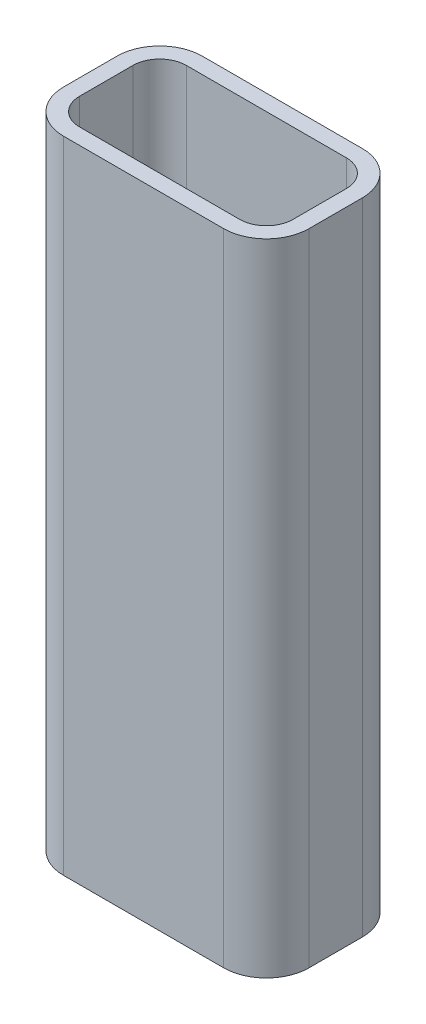
SolidWorks part; units mm, degrees
ref_plane "Front Plane" through (0, 0, 0) normal (0, 0, 1) x (1, 0, 0)
ref_plane "Top Plane" through (0, 0, 0) normal (0, 1, 0) x (1, 0, 0)
ref_plane "Right Plane" through (0, 0, 0) normal (1, 0, 0) x (0, 0, -1)
sketch "Sketch1" plane through (0, 0, 0) normal (0, 1, 0) x (1, 0, 0)
  line L1 (-15, -10) -> (15, -10)
  line L2 (-20, -5) -> (-20, 5)
  line L3 (-15, 10) -> (15, 10)
  line L4 (20, -5) -> (20, 5)
  line L5 (-20, -10) -> (20, 10) construction
  line L6 (-20, 10) -> (20, -10) construction
  arc A0 (15, -10) -> (20, -5) centre (15, -5) ccw
  arc A1 (-15, -10) -> (-20, -5) centre (-15, -5) cw
  arc A2 (-20, 5) -> (-15, 10) centre (-15, 5) cw
  arc A3 (15, 10) -> (20, 5) centre (15, 5) cw
  point P0 (0, 0)
  dimension "D3" = 5
  dimension "with" = 40
  dimension "height" = 20
extrude "Extrude-Thin2" add sketch "Sketch1" along normal blind 120 from offset 60 thin offset against normal yes
sketch "Sketch2" plane through (0, 0, -13) normal (0, 0, -1) x (-1, 0, 0)
  line L0 (0, 45) -> (0, -45) construction
  line L1 (6, 45) -> (6, -45)
  line L2 (-6, 45) -> (-6, -45)
  arc A0 (6, 45) -> (-6, 45) centre (0, 45) ccw
  arc A1 (-6, -45) -> (6, -45) centre (0, -45) ccw
  point P2 (0, 0)
  dimension "D1" = 6
  dimension "D2" = 90
extrude "Cut-Extrude1" [suppressed] cut sketch "Sketch2" against normal blind 120
